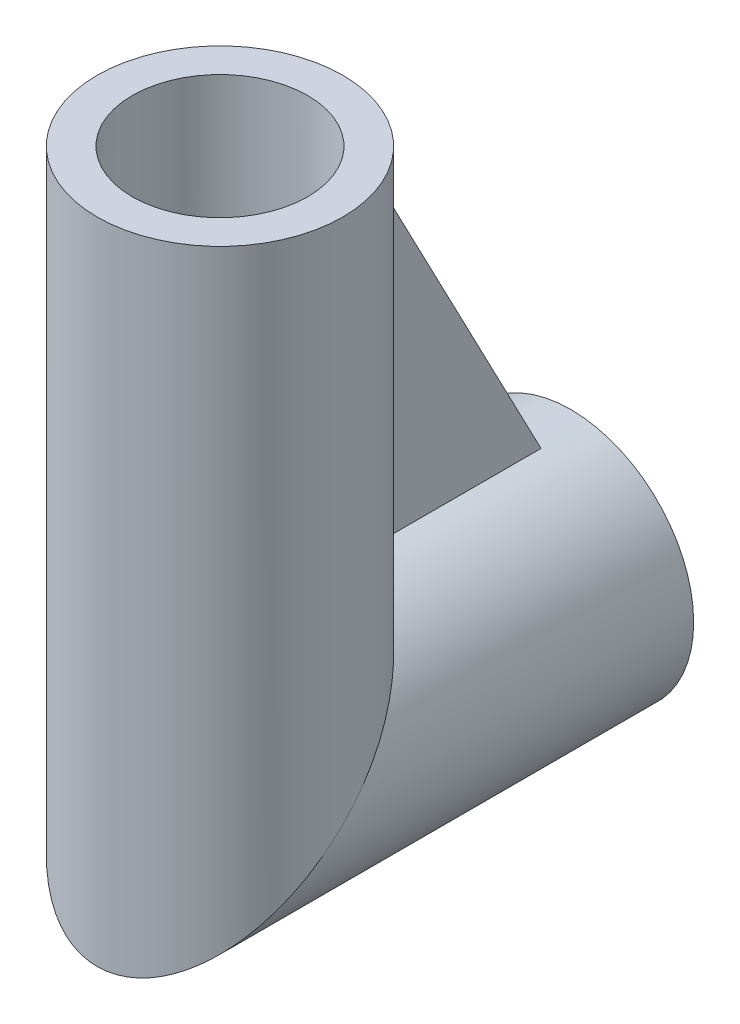
SolidWorks part; units mm, degrees
material "ABS"
ref_plane "Front Plane" through (0, 0, 0) normal (0, 0, 1) x (1, 0, 0)
ref_plane "Top Plane" through (0, 0, 0) normal (0, 1, 0) x (1, 0, 0)
ref_plane "Right Plane" through (0, 0, 0) normal (1, 0, 0) x (0, 0, -1)
sketch "Sketch1" plane through (0, 0, 0) normal (-1, 0, 0) x (0, 0, 1)
  line L0 (0, 0) -> (20, 0)
  line L1 (20, 0) -> (20, 30)
  dimension "D1" = 20
  dimension "D2" = 30
sketch "Sketch2" plane through (0, 0, 0) normal (0, 0, 1) x (1, 0, 0)
  circle A0 centre (0, 0) radius 5
  circle A1 centre (0, 0) radius 7
  dimension "D1" = 10
  dimension "D2" = 14
sweep "Sweep1" add profiles "Sketch2" path "Sketch1"
sketch "Sketch3" plane through (0, 0, 0) normal (1, 0, 0) x (0, 0, -1)
  line L0 (-13.4568, 6.5432) -> (-2.5, 6.5432)
  line L2 (-2.5, 6.5432) -> (-13.4568, 27.5)
  line L4 (-13.4568, 27.5) -> (-13.4568, 6.5432)
  line L5 (0, -7) -> (0, 7) construction
  line L6 (-13, 30) -> (-27, 30) construction
  line L7 (-27, -7) -> (-13, 7) construction
  dimension "D1" = 2.5
  dimension "D2" = 2.5
extrude "Boss-Extrude1" add sketch "Sketch3" along normal mid plane 2
